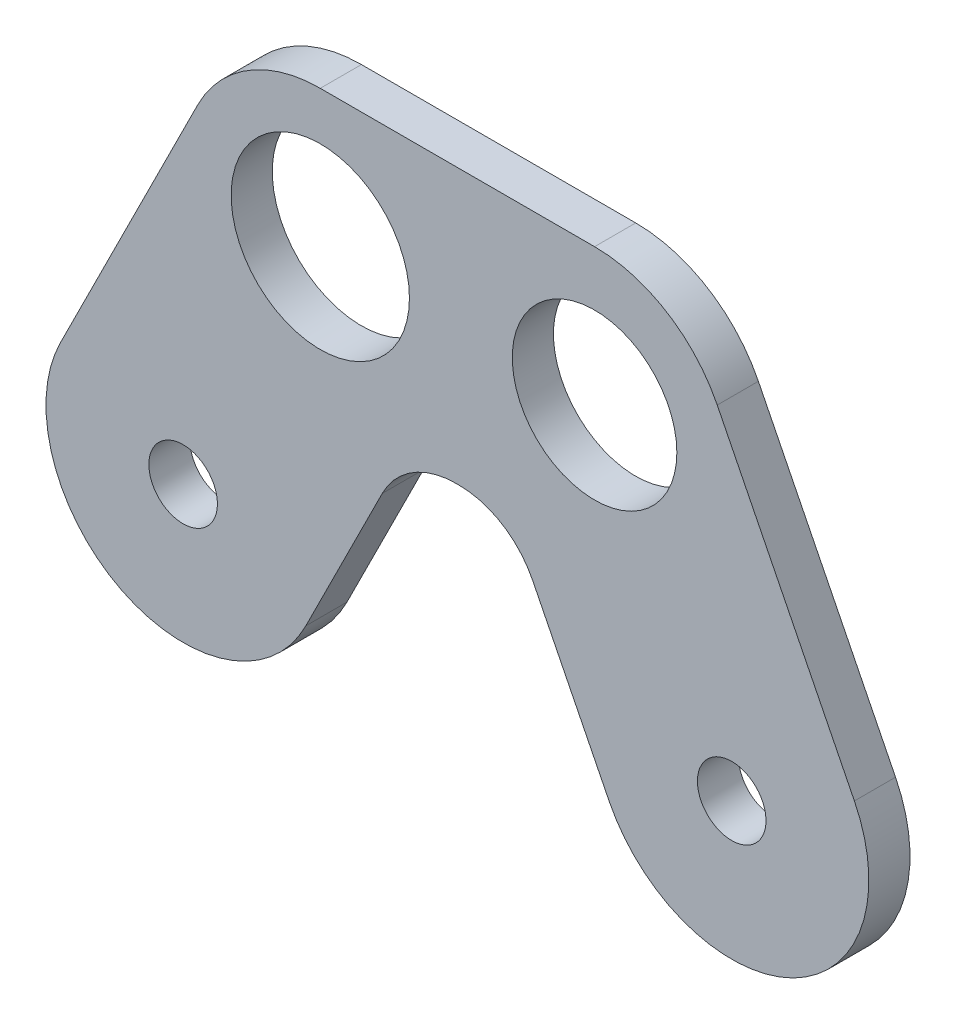
SolidWorks part; units mm, degrees
ref_plane "Plan de face" through (0, 0, 0) normal (0, 0, 1) x (1, 0, 0)
ref_plane "Plan de dessus" through (0, 0, 0) normal (0, 1, 0) x (1, 0, 0)
ref_plane "Plan de droite" through (0, 0, 0) normal (1, 0, 0) x (0, 0, -1)
sketch "Esquisse1" plane through (0, 0, 0) normal (0, 0, 1) x (1, 0, 0)
  line L0 (0, 0) -> (20, 0) construction
  line L1 (-10, -20) -> (30, -20) construction
  line L2 (10, 0) -> (10, -20) construction
  line L5 (0, 10) -> (20, 10)
  line L6 (-18.9443, -15.5279) -> (-8.9443, 4.4721)
  line L7 (28.9443, 4.4721) -> (38.9443, -15.5279)
  line L8 (-1.0557, -24.4721) -> (6.1803, -10)
  line L9 (21.0557, -24.4721) -> (13.8197, -10)
  line L10 (6.1803, -10) -> (13.8197, -10)
  line L11 (6.1803, -10) -> (13.8197, -10) construction
  circle A0 centre (0, 0) radius 6.5
  circle A1 centre (20, 0) radius 6
  circle A2 centre (-10, -20) radius 2.5
  circle A3 centre (30, -20) radius 2.5
  arc A4 (-18.9443, -15.5279) -> (-1.0557, -24.4721) centre (-10, -20) ccw
  arc A5 (21.0557, -24.4721) -> (38.9443, -15.5279) centre (30, -20) ccw
  arc A7 (28.9443, 4.4721) -> (20, 10) centre (20, 0) ccw
  arc A8 (0, 10) -> (-8.9443, 4.4721) centre (0, 0) ccw
  point P9 (0, 0)
  dimension "D1" = 13
  dimension "D2" = 12
  dimension "D6" = 5
  dimension "D5" = 10
  dimension "D8" = 10
  dimension "D9" = 10
  dimension "D3" = 20
  dimension "D4" = 20
  dimension "D7" = 40
extrude "Boss.-Extru.1" add sketch "Esquisse1" along normal blind 3
fillet "Congé1" radius 6 2 edges at (13.8197, -10, 1.5) (6.1803, -10, 1.5)
